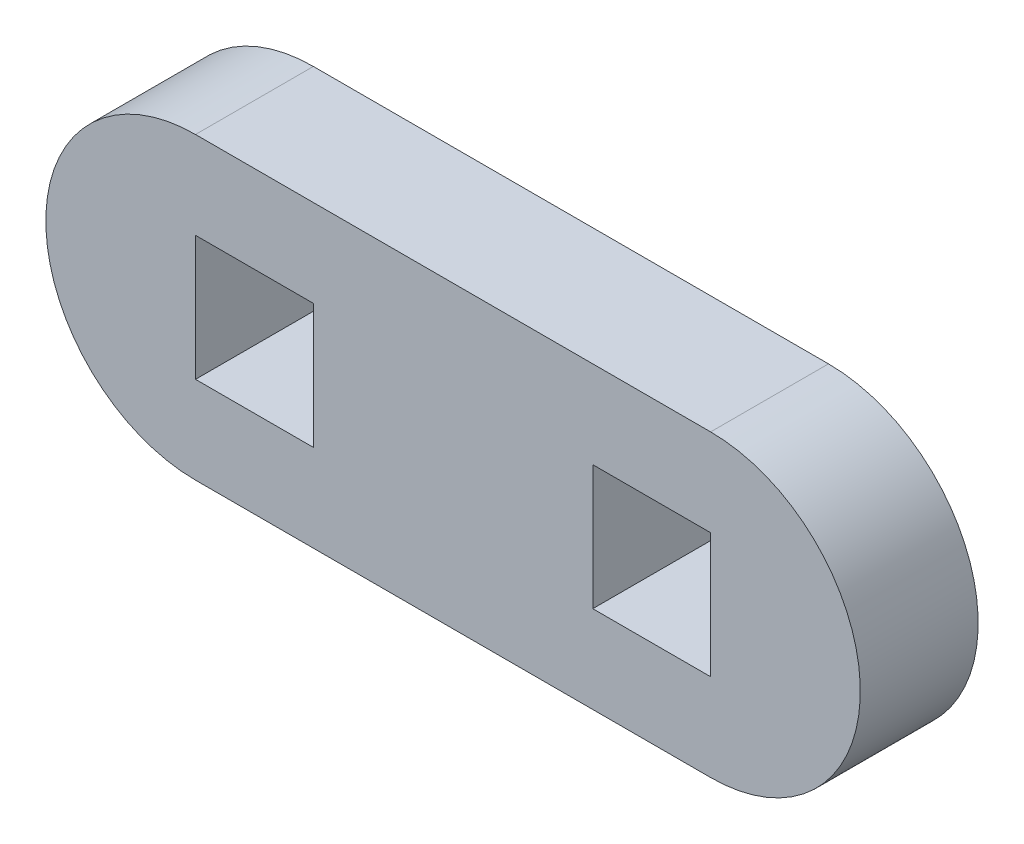
SolidWorks part; units mm, degrees
ref_plane "Front Plane" through (0, 0, 0) normal (0, 0, 1) x (1, 0, 0)
ref_plane "Top Plane" through (0, 0, 0) normal (0, 1, 0) x (1, 0, 0)
ref_plane "Right Plane" through (0, 0, 0) normal (1, 0, 0) x (0, 0, -1)
sketch "Sketch2" plane through (0, 0, 0) normal (0, 0, 1) x (1, 0, 0)
  line L0 (297.8899, 54.3694) -> (324.1139, 54.3694) construction
  line L1 (297.8899, 57.5444) -> (303.8899, 57.5444)
  line L2 (297.8899, 57.5444) -> (297.8899, 51.1944)
  line L3 (297.8899, 51.1944) -> (303.8899, 51.1944)
  line L4 (303.8899, 57.5444) -> (303.8899, 51.1944)
  line L5 (318.1139, 57.5444) -> (324.1139, 57.5444)
  line L6 (318.1139, 57.5444) -> (318.1139, 51.1944)
  line L7 (318.1139, 51.1944) -> (324.1139, 51.1944)
  line L8 (324.1139, 57.5444) -> (324.1139, 51.1944)
  line L9 (297.8899, 61.9894) -> (324.1139, 61.9894)
  line L10 (297.8899, 46.7494) -> (324.1139, 46.7494)
  arc A0 (297.8899, 61.9894) -> (297.8899, 46.7494) centre (297.8899, 54.3694) ccw
  arc A1 (324.1139, 46.7494) -> (324.1139, 61.9894) centre (324.1139, 54.3694) ccw
  point P14 (311.0019, 54.3694)
extrude "Boss-Extrude1" add sketch "Sketch2" along normal blind 6
